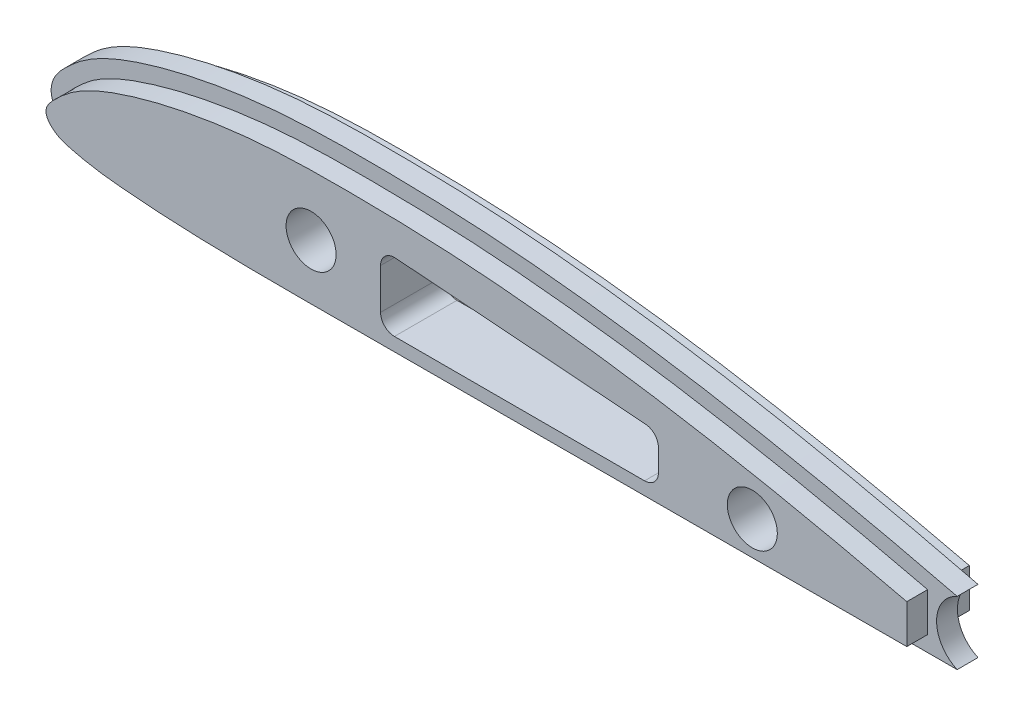
SolidWorks part; units mm, degrees
ref_plane "Front Plane" through (0, 0, 0) normal (0, 0, 1) x (1, 0, 0)
ref_plane "Top Plane" through (0, 0, 0) normal (0, 1, 0) x (1, 0, 0)
ref_plane "Right Plane" through (0, 0, 0) normal (1, 0, 0) x (0, 0, -1)
sketch "Sketch3" plane through (0, 0, 36) normal (0, 0, 1) x (1, 0, 0)
  line L0 (-17.5077, 7.0986) -> (-17.5077, -2.034) construction
  line L1 (-17.5077, 7.0986) -> (-17.5077, -2.034)
  circle A0 centre (-107.5077, 7.9994) radius 3.5 construction
  circle A1 centre (-107.5077, 7.9994) radius 3.5
  spline S0 degree 3 poles (2578.6537, 5862.2825) (2014.027, -6.3495) (990.936, -0.1904) (-36.5554, -2.0685) (-52.2047, -2.0959) (-64.7243, -2.119) (-74.1141, -2.1361) (-83.5035, -2.1545) (-92.8956, -2.1673) (-100.7151, -2.1812) (-106.9759, -2.2038) (-111.6807, -2.2071) (-116.3926, -2.1785) (-121.1131, -2.1002) (-125.8432, -1.946) (-129.7876, -1.7371) (-132.9528, -1.4988) (-135.2992, -1.2986) (-137.3062, -1.095) (-138.941, -0.8588) (-140.1679, -0.6381) (-141.3883, -0.367) (-142.5078, -0.1069) (-143.6199, 0.1874) (-144.5733, 0.5667) (-145.3185, 0.9606) (-146.0045, 1.4531) (-146.6187, 2.0134) (-147.1053, 2.5935) (-147.4573, 3.1709) (-147.6837, 3.6454) (-147.8752, 4.2833) (-147.9432, 4.9253) (-147.8905, 5.6127) (-147.6734, 6.4007) (-147.2979, 7.1351) (-146.8042, 7.8185) (-146.3098, 8.3773) (-145.6675, 9.0171) (-144.9341, 9.694) (-143.9278, 10.5554) (-142.8506, 11.3324) (-141.7288, 12.0232) (-140.2222, 12.8248) (-138.3122, 13.6733) (-136.0049, 14.5197) (-133.7043, 15.2528) (-131.3815, 15.9138) (-128.2582, 16.6871) (-124.3362, 17.4725) (-119.6006, 18.1902) (-114.8231, 18.6719) (-108.4622, 19.0054) (-100.5785, 19.0321) (-91.1325, 18.8431) (-81.6696, 18.2776) (-69.1255, 17.0496) (-53.5308, 14.8273) (539.3666, -100.5985) (899.837, -1164.8591) (3202.4957, 5810.2231) knots -10.067578 -10.067578 -10.067578 -10.067578 0.066238 0.128738 0.191238 0.222488 0.253738 0.284988 0.316238 0.347488 0.363113 0.378738 0.394363 0.409988 0.425613 0.441238 0.44905 0.456863 0.464675 0.468581 0.472488 0.476394 0.4803 0.484206 0.48616 0.488113 0.490066 0.492019 0.493972 0.494949 0.495925 0.496902 0.497878 0.498855 0.499831 0.501785 0.503738 0.505691 0.507644 0.51155 0.515456 0.519363 0.523269 0.527175 0.534988 0.5428 0.550613 0.558425 0.566238 0.581863 0.597488 0.613113 0.628738 0.659988 0.691238 0.722488 0.753738 0.816238 0.878738 6.758162 6.758162 6.758162 6.758162 only from (-17.5077, -2.034) to (-17.5077, 7.0986) construction
  spline S1 degree 3 poles (-17.5077, -2.034) (-17.5971, -2.0342) (-23.9464, -2.0455) (-36.5554, -2.0685) (-52.2047, -2.0959) (-64.7243, -2.119) (-74.1141, -2.1361) (-83.5035, -2.1545) (-92.8956, -2.1673) (-100.7151, -2.1812) (-106.9759, -2.2038) (-111.6807, -2.2071) (-116.3926, -2.1785) (-121.1131, -2.1002) (-125.8432, -1.946) (-129.7876, -1.7371) (-132.9528, -1.4988) (-135.2992, -1.2986) (-137.3062, -1.095) (-138.941, -0.8588) (-140.1679, -0.6381) (-141.3883, -0.367) (-142.5078, -0.1069) (-143.6199, 0.1874) (-144.5733, 0.5667) (-145.3185, 0.9606) (-146.0045, 1.4531) (-146.6187, 2.0134) (-147.1053, 2.5935) (-147.4573, 3.1709) (-147.6837, 3.6454) (-147.8752, 4.2833) (-147.9432, 4.9253) (-147.8905, 5.6127) (-147.6734, 6.4007) (-147.2979, 7.1351) (-146.8042, 7.8185) (-146.3098, 8.3773) (-145.6675, 9.0171) (-144.9341, 9.694) (-143.9278, 10.5554) (-142.8506, 11.3324) (-141.7288, 12.0232) (-140.2222, 12.8248) (-138.3122, 13.6733) (-136.0049, 14.5197) (-133.7043, 15.2528) (-131.3815, 15.9138) (-128.2582, 16.6871) (-124.3362, 17.4725) (-119.6006, 18.1902) (-114.8231, 18.6719) (-108.4622, 19.0054) (-100.5785, 19.0321) (-91.1325, 18.8431) (-81.6696, 18.2776) (-69.1255, 17.0496) (-53.5308, 14.8273) (-35.2974, 11.2776) (-23.331, 8.5279) (-17.5077, 7.0986) knots 0.065345 0.065345 0.065345 0.065345 0.066238 0.128738 0.191238 0.222488 0.253738 0.284988 0.316238 0.347488 0.363113 0.378738 0.394363 0.409988 0.425613 0.441238 0.44905 0.456863 0.464675 0.468581 0.472488 0.476394 0.4803 0.484206 0.48616 0.488113 0.490066 0.492019 0.493972 0.494949 0.495925 0.496902 0.497878 0.498855 0.499831 0.501785 0.503738 0.505691 0.507644 0.51155 0.515456 0.519363 0.523269 0.527175 0.534988 0.5428 0.550613 0.558425 0.566238 0.581863 0.597488 0.613113 0.628738 0.659988 0.691238 0.722488 0.753738 0.816238 0.878738 0.938393 0.938393 0.938393 0.938393
extrude "Boss-Extrude1" add sketch "Sketch3" along normal blind 4
sketch "Sketch4" plane through (0, 0, 40) normal (0, 0, 1) x (1, 0, 0)
  line L8 (-19.5077, -0.0375) -> (-19.5077, 5.5292) construction
  line L9 (-19.5077, -0.0375) -> (-19.5077, 5.5292)
  spline S0 degree 3 poles (7588.3721, 24816.6865) (508.1583, -325.7078) (274.7285, -72.9604) (-8.7039, 2.8051) (-14.5294, 4.3114) (-20.3656, 5.749) (-27.1741, 7.349) (-33.9781, 8.8726) (-44.6779, 11.0739) (-57.3308, 13.3728) (-71.0095, 15.2439) (-80.7996, 16.1817) (-89.6088, 16.7577) (-95.4883, 16.9494) (-102.3503, 17.0132) (-107.258, 17.0037) (-112.1692, 16.8306) (-117.0923, 16.4612) (-121.0358, 15.9731) (-125.9769, 15.1312) (-129.9439, 14.2596) (-133.8889, 13.1136) (-136.8933, 12.0983) (-139.3897, 11.029) (-141.3837, 9.9199) (-142.7986, 8.9179) (-143.8683, 7.9575) (-144.6863, 7.1841) (-145.2085, 6.616) (-145.5978, 6.0643) (-145.813, 5.6279) (-145.9496, 5.1105) (-145.9171, 4.6811) (-145.7813, 4.3037) (-145.6317, 4.0021) (-145.3221, 3.5593) (-144.843, 3.0846) (-144.0891, 2.535) (-143.0082, 2.0734) (-141.6202, 1.743) (-140.1624, 1.3998) (-138.7, 1.1241) (-136.7482, 0.848) (-134.3019, 0.6215) (-131.3684, 0.3793) (-125.498, 0.0064) (-115.6953, -0.2455) (-101.9687, -0.1771) (-89.2206, -0.1643) (-73.5301, -0.1352) (-57.8396, -0.1062) (-42.149, -0.0778) (-31.3617, -0.0594) (-22.5358, -0.0426) (-13.7099, -0.0276) (702.9944, 1.3342) (1416.7931, -17.4986) (2080.9229, 25690.8936) knots -2.879038 -2.879038 -2.879038 -2.879038 0.020105 0.030145 0.050191 0.08018 0.090156 0.12002 0.149793 0.199219 0.248396 0.287604 0.297393 0.336535 0.346322 0.365908 0.385531 0.395376 0.415192 0.425184 0.445412 0.455711 0.466191 0.477055 0.482787 0.488946 0.494316 0.497126 0.500187 0.502001 0.50385 0.50502 0.507318 0.507987 0.509024 0.510668 0.513358 0.515716 0.519949 0.524973 0.529954 0.534903 0.539824 0.54963 0.559425 0.569214 0.608356 0.657307 0.706263 0.735637 0.813967 0.862923 0.892297 0.92167 0.951044 0.980418 8.077484 8.077484 8.077484 8.077484 only from (1.0061, 0.1754) to (1, -0.0006) construction
  spline S1 degree 3 poles (-19.5077, 5.5292) (-20.4438, 5.7568) (-22.3518, 6.2157) (-27.1741, 7.349) (-33.9781, 8.8726) (-44.6779, 11.0739) (-57.3308, 13.3728) (-71.0095, 15.2439) (-80.7996, 16.1817) (-89.6088, 16.7577) (-95.4883, 16.9494) (-102.3503, 17.0132) (-107.258, 17.0037) (-112.1692, 16.8306) (-117.0923, 16.4612) (-121.0358, 15.9731) (-125.9769, 15.1312) (-129.9439, 14.2596) (-133.8889, 13.1136) (-136.8933, 12.0983) (-139.3897, 11.029) (-141.3837, 9.9199) (-142.7986, 8.9179) (-143.8683, 7.9575) (-144.6863, 7.1841) (-145.2085, 6.616) (-145.5978, 6.0643) (-145.813, 5.6279) (-145.9496, 5.1105) (-145.9171, 4.6811) (-145.7813, 4.3037) (-145.6317, 4.0021) (-145.3221, 3.5593) (-144.843, 3.0846) (-144.0891, 2.535) (-143.0082, 2.0734) (-141.6202, 1.743) (-140.1624, 1.3998) (-138.7, 1.1241) (-136.7482, 0.848) (-134.3019, 0.6215) (-131.3684, 0.3793) (-125.498, 0.0064) (-115.6953, -0.2455) (-101.9687, -0.1771) (-89.2206, -0.1643) (-73.5301, -0.1352) (-57.8396, -0.1062) (-42.149, -0.0778) (-31.3617, -0.0594) (-24.4684, -0.0463) (-20.5171, -0.0393) (-19.5077, -0.0375) knots 0.070562 0.070562 0.070562 0.070562 0.08018 0.090156 0.12002 0.149793 0.199219 0.248396 0.287604 0.297393 0.336535 0.346322 0.365908 0.385531 0.395376 0.415192 0.425184 0.445412 0.455711 0.466191 0.477055 0.482787 0.488946 0.494316 0.497126 0.500187 0.502001 0.50385 0.50502 0.507318 0.507987 0.509024 0.510668 0.513358 0.515716 0.519949 0.524973 0.529954 0.534903 0.539824 0.54963 0.559425 0.569214 0.608356 0.657307 0.706263 0.735637 0.813967 0.862923 0.892297 0.92167 0.931748 0.931748 0.931748 0.931748
extrude "Boss-Extrude2" add sketch "Sketch4" along normal blind 3
sketch "Sketch6" plane through (0, 0, 40) normal (0, 0, 1) x (1, 0, 0)
  line L1 (-17.5077, -2.034) -> (-17.5077, 7.0986)
  line L2 (-17.5077, -2.034) -> (-17.5077, 7.0986)
  spline S1 degree 3 poles (1849.108, 2047.2656) (715.5466, -712.3066) (399.8034, -73.4282) (-53.5308, 14.8273) (-69.1255, 17.0496) (-81.6696, 18.2776) (-91.1325, 18.8431) (-100.5785, 19.0321) (-108.4622, 19.0054) (-114.8231, 18.6719) (-119.6006, 18.1902) (-124.3362, 17.4725) (-128.2582, 16.6871) (-131.3815, 15.9138) (-133.7043, 15.2528) (-136.0049, 14.5197) (-138.3122, 13.6733) (-140.2222, 12.8248) (-141.7288, 12.0232) (-142.8506, 11.3324) (-143.9278, 10.5554) (-144.9341, 9.694) (-145.6675, 9.0171) (-146.3098, 8.3773) (-146.8042, 7.8185) (-147.2979, 7.1351) (-147.6734, 6.4007) (-147.8905, 5.6127) (-147.9432, 4.9253) (-147.8752, 4.2833) (-147.6837, 3.6454) (-147.4573, 3.1709) (-147.1053, 2.5935) (-146.6187, 2.0134) (-146.0045, 1.4531) (-145.3185, 0.9606) (-144.5733, 0.5667) (-143.6199, 0.1874) (-142.5078, -0.1069) (-141.3883, -0.367) (-140.1679, -0.6381) (-138.941, -0.8588) (-137.3062, -1.095) (-135.2992, -1.2986) (-132.9528, -1.4988) (-129.7876, -1.7371) (-125.8432, -1.946) (-121.1131, -2.1002) (-116.3926, -2.1785) (-111.6807, -2.2071) (-106.9759, -2.2038) (-100.7151, -2.1812) (-92.8956, -2.1673) (-83.5035, -2.1545) (-74.1141, -2.1361) (-64.7243, -2.119) (-52.2047, -2.0959) (-36.5554, -2.0685) (675.8455, -0.7663) (1382.8755, -3.3128) (1935.6442, 1919.1904) knots -4.341032 -4.341032 -4.341032 -4.341032 0.125 0.1875 0.25 0.28125 0.3125 0.34375 0.375 0.390625 0.40625 0.421875 0.4375 0.445312 0.453125 0.460937 0.46875 0.476562 0.480469 0.484375 0.488281 0.492187 0.496094 0.498047 0.5 0.501953 0.503906 0.504883 0.505859 0.506836 0.507812 0.508789 0.509766 0.511719 0.513672 0.515625 0.517578 0.519531 0.523438 0.527344 0.53125 0.535156 0.539062 0.546875 0.554688 0.5625 0.578125 0.59375 0.609375 0.625 0.640625 0.65625 0.6875 0.71875 0.75 0.78125 0.8125 0.875 0.9375 7.925347 7.925347 7.925347 7.925347 only from (-17.5077, 7.0986) to (-17.5077, -2.034)
  spline S2 degree 3 poles (-17.5077, 7.0986) (-23.331, 8.5279) (-35.2974, 11.2776) (-53.5308, 14.8273) (-69.1255, 17.0496) (-81.6696, 18.2776) (-91.1325, 18.8431) (-100.5785, 19.0321) (-108.4622, 19.0054) (-114.8231, 18.6719) (-119.6006, 18.1902) (-124.3362, 17.4725) (-128.2582, 16.6871) (-131.3815, 15.9138) (-133.7043, 15.2528) (-136.0049, 14.5197) (-138.3122, 13.6733) (-140.2222, 12.8248) (-141.7288, 12.0232) (-142.8506, 11.3324) (-143.9278, 10.5554) (-144.9341, 9.694) (-145.6675, 9.0171) (-146.3098, 8.3773) (-146.8042, 7.8185) (-147.2979, 7.1351) (-147.6734, 6.4007) (-147.8905, 5.6127) (-147.9432, 4.9253) (-147.8752, 4.2833) (-147.6837, 3.6454) (-147.4573, 3.1709) (-147.1053, 2.5935) (-146.6187, 2.0134) (-146.0045, 1.4531) (-145.3185, 0.9606) (-144.5733, 0.5667) (-143.6199, 0.1874) (-142.5078, -0.1069) (-141.3883, -0.367) (-140.1679, -0.6381) (-138.941, -0.8588) (-137.3062, -1.095) (-135.2992, -1.2986) (-132.9528, -1.4988) (-129.7876, -1.7371) (-125.8432, -1.946) (-121.1131, -2.1002) (-116.3926, -2.1785) (-111.6807, -2.2071) (-106.9759, -2.2038) (-100.7151, -2.1812) (-92.8956, -2.1673) (-83.5035, -2.1545) (-74.1141, -2.1361) (-64.7243, -2.119) (-52.2047, -2.0959) (-36.5554, -2.0685) (-23.9464, -2.0455) (-17.5971, -2.0342) (-17.5077, -2.034) knots 0.065345 0.065345 0.065345 0.065345 0.125 0.1875 0.25 0.28125 0.3125 0.34375 0.375 0.390625 0.40625 0.421875 0.4375 0.445312 0.453125 0.460937 0.46875 0.476562 0.480469 0.484375 0.488281 0.492187 0.496094 0.498047 0.5 0.501953 0.503906 0.504883 0.505859 0.506836 0.507812 0.508789 0.509766 0.511719 0.513672 0.515625 0.517578 0.519531 0.523438 0.527344 0.53125 0.535156 0.539062 0.546875 0.554688 0.5625 0.578125 0.59375 0.609375 0.625 0.640625 0.65625 0.6875 0.71875 0.75 0.78125 0.8125 0.875 0.9375 0.938393 0.938393 0.938393 0.938393
  dimension "D1" = 0
extrude "Cut-Extrude1" cut sketch "Sketch6" against normal through all
sketch "Sketch7" plane through (0, 0, 40) normal (0, 0, -1) x (-1, 0, 0)
  line L0 (17.5077, 7.0986) -> (17.5077, -2.034) construction
  line L1 (17.5077, 7.0986) -> (17.5077, -2.034)
  spline S0 degree 3 poles (-1935.6474, 1919.198) (-1382.8774, -3.3129) (-675.8464, -0.7663) (36.5554, -2.0685) (52.2047, -2.0959) (64.7243, -2.119) (74.1141, -2.1361) (83.5035, -2.1545) (92.8956, -2.1673) (100.7151, -2.1812) (106.9759, -2.2038) (111.6807, -2.2071) (116.3926, -2.1785) (121.1131, -2.1002) (125.8432, -1.946) (129.7876, -1.7371) (132.9528, -1.4988) (135.2992, -1.2986) (137.3062, -1.095) (138.941, -0.8588) (140.1679, -0.6381) (141.3883, -0.367) (142.5078, -0.1069) (143.6199, 0.1874) (144.5733, 0.5667) (145.3185, 0.9606) (146.0045, 1.4531) (146.6187, 2.0134) (147.1053, 2.5935) (147.4573, 3.1709) (147.6837, 3.6454) (147.8752, 4.2833) (147.9432, 4.9253) (147.8905, 5.6127) (147.6734, 6.4007) (147.2979, 7.1351) (146.8042, 7.8185) (146.3098, 8.3773) (145.6675, 9.0171) (144.9341, 9.694) (143.9278, 10.5554) (142.8506, 11.3324) (141.7288, 12.0232) (140.2222, 12.8248) (138.3122, 13.6733) (136.0049, 14.5197) (133.7043, 15.2528) (131.3815, 15.9138) (128.2582, 16.6871) (124.3362, 17.4725) (119.6006, 18.1902) (114.8231, 18.6719) (108.4622, 19.0054) (100.5785, 19.0321) (91.1325, 18.8431) (81.6696, 18.2776) (69.1255, 17.0496) (53.5308, 14.8273) (-399.8012, -73.4278) (-715.5435, -712.3002) (-1849.0908, 2047.2238) knots -6.921618 -6.921618 -6.921618 -6.921618 0.066238 0.128738 0.191238 0.222488 0.253738 0.284988 0.316238 0.347488 0.363113 0.378738 0.394363 0.409988 0.425613 0.441238 0.44905 0.456863 0.464675 0.468581 0.472488 0.476394 0.4803 0.484206 0.48616 0.488113 0.490066 0.492019 0.493972 0.494949 0.495925 0.496902 0.497878 0.498855 0.499831 0.501785 0.503738 0.505691 0.507644 0.51155 0.515456 0.519363 0.523269 0.527175 0.534988 0.5428 0.550613 0.558425 0.566238 0.581863 0.597488 0.613113 0.628738 0.659988 0.691238 0.722488 0.753738 0.816238 0.878738 5.344747 5.344747 5.344747 5.344747 only from (17.5077, -2.034) to (17.5077, 7.0986) construction
  spline S1 degree 3 poles (17.5077, -2.034) (17.5971, -2.0342) (23.9464, -2.0455) (36.5554, -2.0685) (52.2047, -2.0959) (64.7243, -2.119) (74.1141, -2.1361) (83.5035, -2.1545) (92.8956, -2.1673) (100.7151, -2.1812) (106.9759, -2.2038) (111.6807, -2.2071) (116.3926, -2.1785) (121.1131, -2.1002) (125.8432, -1.946) (129.7876, -1.7371) (132.9528, -1.4988) (135.2992, -1.2986) (137.3062, -1.095) (138.941, -0.8588) (140.1679, -0.6381) (141.3883, -0.367) (142.5078, -0.1069) (143.6199, 0.1874) (144.5733, 0.5667) (145.3185, 0.9606) (146.0045, 1.4531) (146.6187, 2.0134) (147.1053, 2.5935) (147.4573, 3.1709) (147.6837, 3.6454) (147.8752, 4.2833) (147.9432, 4.9253) (147.8905, 5.6127) (147.6734, 6.4007) (147.2979, 7.1351) (146.8042, 7.8185) (146.3098, 8.3773) (145.6675, 9.0171) (144.9341, 9.694) (143.9278, 10.5554) (142.8506, 11.3324) (141.7288, 12.0232) (140.2222, 12.8248) (138.3122, 13.6733) (136.0049, 14.5197) (133.7043, 15.2528) (131.3815, 15.9138) (128.2582, 16.6871) (124.3362, 17.4725) (119.6006, 18.1902) (114.8231, 18.6719) (108.4622, 19.0054) (100.5785, 19.0321) (91.1325, 18.8431) (81.6696, 18.2776) (69.1255, 17.0496) (53.5308, 14.8273) (35.2974, 11.2776) (23.331, 8.5279) (17.5077, 7.0986) knots 0.065345 0.065345 0.065345 0.065345 0.066238 0.128738 0.191238 0.222488 0.253738 0.284988 0.316238 0.347488 0.363113 0.378738 0.394363 0.409988 0.425613 0.441238 0.44905 0.456863 0.464675 0.468581 0.472488 0.476394 0.4803 0.484206 0.48616 0.488113 0.490066 0.492019 0.493972 0.494949 0.495925 0.496902 0.497878 0.498855 0.499831 0.501785 0.503738 0.505691 0.507644 0.51155 0.515456 0.519363 0.523269 0.527175 0.534988 0.5428 0.550613 0.558425 0.566238 0.581863 0.597488 0.613113 0.628738 0.659988 0.691238 0.722488 0.753738 0.816238 0.878738 0.938393 0.938393 0.938393 0.938393
extrude "Boss-Extrude4" add sketch "Sketch7" along normal blind 3
sketch "Sketch8" plane through (0, 0, 37) normal (0, 0, -1) x (-1, 0, 0)
  line L1 (19.5077, 5.5292) -> (19.5077, -0.0375)
  line L2 (19.5077, 5.5292) -> (19.5077, -0.0375)
  spline S1 degree 3 poles (-1386.8586, 2447.2657) (-920.0116, -6.1198) (-445.7888, 0.849) (31.3617, -0.0594) (42.149, -0.0778) (57.8396, -0.1062) (73.5301, -0.1352) (89.2206, -0.1643) (101.9687, -0.1771) (115.6953, -0.2455) (125.498, 0.0064) (131.3684, 0.3793) (134.3019, 0.6215) (136.7482, 0.848) (138.7, 1.1241) (140.1624, 1.3998) (141.6202, 1.743) (143.0082, 2.0734) (144.0891, 2.535) (144.843, 3.0846) (145.3221, 3.5593) (145.6317, 4.0021) (145.7813, 4.3037) (145.9171, 4.6811) (145.9496, 5.1105) (145.813, 5.6279) (145.5978, 6.0643) (145.2085, 6.616) (144.6863, 7.1841) (143.8683, 7.9575) (142.7986, 8.9179) (141.3837, 9.9199) (139.3897, 11.029) (136.8933, 12.0983) (133.8889, 13.1136) (129.9439, 14.2596) (125.9769, 15.1312) (121.0358, 15.9731) (117.0923, 16.4612) (112.1692, 16.8306) (107.258, 17.0037) (102.3503, 17.0132) (95.4883, 16.9494) (89.6088, 16.7577) (80.7996, 16.1817) (71.0095, 15.2439) (57.3308, 13.3728) (44.6779, 11.0739) (33.9781, 8.8726) (27.1741, 7.349) (-277.492, -64.2503) (-519.7765, -384.6594) (-1220.5185, 2634.6577) knots -4.624642 -4.624642 -4.624642 -4.624642 0.08064 0.110014 0.139387 0.188343 0.266673 0.296047 0.345003 0.393954 0.433096 0.442885 0.45268 0.462486 0.467407 0.472356 0.477337 0.482361 0.486594 0.488952 0.491642 0.493286 0.494324 0.494992 0.49729 0.49846 0.500309 0.502123 0.505184 0.507994 0.513364 0.519523 0.525256 0.536119 0.546599 0.556898 0.577126 0.587118 0.606934 0.616779 0.636402 0.655988 0.665775 0.704917 0.714706 0.753914 0.803091 0.852517 0.88229 0.912154 0.92213 4.007029 4.007029 4.007029 4.007029 only from (19.5077, -0.0375) to (19.5077, 5.5292)
  spline S2 degree 3 poles (19.5077, -0.0375) (20.5171, -0.0393) (24.4684, -0.0463) (31.3617, -0.0594) (42.149, -0.0778) (57.8396, -0.1062) (73.5301, -0.1352) (89.2206, -0.1643) (101.9687, -0.1771) (115.6953, -0.2455) (125.498, 0.0064) (131.3684, 0.3793) (134.3019, 0.6215) (136.7482, 0.848) (138.7, 1.1241) (140.1624, 1.3998) (141.6202, 1.743) (143.0082, 2.0734) (144.0891, 2.535) (144.843, 3.0846) (145.3221, 3.5593) (145.6317, 4.0021) (145.7813, 4.3037) (145.9171, 4.6811) (145.9496, 5.1105) (145.813, 5.6279) (145.5978, 6.0643) (145.2085, 6.616) (144.6863, 7.1841) (143.8683, 7.9575) (142.7986, 8.9179) (141.3837, 9.9199) (139.3897, 11.029) (136.8933, 12.0983) (133.8889, 13.1136) (129.9439, 14.2596) (125.9769, 15.1312) (121.0358, 15.9731) (117.0923, 16.4612) (112.1692, 16.8306) (107.258, 17.0037) (102.3503, 17.0132) (95.4883, 16.9494) (89.6088, 16.7577) (80.7996, 16.1817) (71.0095, 15.2439) (57.3308, 13.3728) (44.6779, 11.0739) (33.9781, 8.8726) (27.1741, 7.349) (22.3518, 6.2157) (20.4438, 5.7568) (19.5077, 5.5292) knots 0.070562 0.070562 0.070562 0.070562 0.08064 0.110014 0.139387 0.188343 0.266673 0.296047 0.345003 0.393954 0.433096 0.442885 0.45268 0.462486 0.467407 0.472356 0.477337 0.482361 0.486594 0.488952 0.491642 0.493286 0.494324 0.494992 0.49729 0.49846 0.500309 0.502123 0.505184 0.507994 0.513364 0.519523 0.525256 0.536119 0.546599 0.556898 0.577126 0.587118 0.606934 0.616779 0.636402 0.655988 0.665775 0.704917 0.714706 0.753914 0.803091 0.852517 0.88229 0.912154 0.92213 0.931748 0.931748 0.931748 0.931748
  dimension "D1" = 0
extrude "Boss-Extrude5" add sketch "Sketch8" along normal blind 3
sketch "Sketch9" plane through (0, 0, 43) normal (0, 0, 1) x (1, 0, 0)
  line L0 (-59.5077, 1.9994) -> (-95.5077, 1.9994) construction
  line L1 (-95.3581, 11.8382) -> (-59.3581, 9.1382) construction
  line L2 (-97.5077, 3.9994) -> (-97.5077, 9.8438) construction
  line L3 (-59.5077, 1.9994) -> (-95.5077, 1.9994)
  line L4 (-95.3581, 11.8382) -> (-59.3581, 9.1382)
  line L5 (-97.5077, 3.9994) -> (-97.5077, 9.8438)
  line L6 (-57.5077, 7.1438) -> (-57.5077, 3.9994) construction
  line L7 (-57.5077, 7.1438) -> (-57.5077, 3.9994)
  circle A1 centre (-107.5077, 7.9994) radius 3.6
  arc A2 (-57.5077, 7.1438) -> (-59.3581, 9.1382) centre (-59.5077, 7.1438) ccw construction
  arc A3 (-59.5077, 1.9994) -> (-57.5077, 3.9994) centre (-59.5077, 3.9994) ccw construction
  arc A4 (-97.5077, 3.9994) -> (-95.5077, 1.9994) centre (-95.5077, 3.9994) ccw construction
  arc A5 (-95.3581, 11.8382) -> (-97.5077, 9.8438) centre (-95.5077, 9.8438) ccw construction
  arc A6 (-57.5077, 7.1438) -> (-59.3581, 9.1382) centre (-59.5077, 7.1438) ccw
  arc A7 (-59.5077, 1.9994) -> (-57.5077, 3.9994) centre (-59.5077, 3.9994) ccw
  arc A8 (-97.5077, 3.9994) -> (-95.5077, 1.9994) centre (-95.5077, 3.9994) ccw
  arc A9 (-95.3581, 11.8382) -> (-97.5077, 9.8438) centre (-95.5077, 9.8438) ccw
  circle A11 centre (-43.9939, 4.9994) radius 3.6
extrude "Cut-Extrude2" cut sketch "Sketch9" against normal up to surface (9 mm away) up to face at (-82.6927, 3.6746, 34)
sketch "Sketch10" plane through (0, 0, 40) normal (0, 0, 1) x (1, 0, 0)
  line L0 (-17.5077, 7.0986) -> (-17.5077, -2.034)
  arc A0 (-17.5077, 7.0986) -> (-17.5077, -2.034) centre (-15.4708, 2.5323) ccw construction
  arc A1 (-17.5077, 7.0986) -> (-17.5077, -2.034) centre (-15.4708, 2.5323) ccw
extrude "Cut-Extrude3" cut sketch "Sketch10" against normal through all both and the other way through all
sketch "Sketch11" plane through (0, 0, 43) normal (0, 0, 1) x (1, 0, 0)
  line L0 (-21.5077, 6.6228) -> (-21.5077, -0.5387)
  line L3 (-19.3398, -0.5387) -> (-19.3398, 6.6228)
  line L4 (-21.5077, 6.6228) -> (-19.3398, 6.6228)
  line L5 (-21.5077, -0.5387) -> (-19.3398, -0.5387)
extrude "Cut-Extrude6" cut sketch "Sketch11" against normal up to surface (3 mm away) up to face at (-18.7848, 2.8426, 40)
sketch "Sketch12" plane through (0, 0, 34) normal (0, 0, -1) x (-1, 0, 0)
  line L4 (21.5077, -0.5387) -> (21.5077, 6.6228)
  line L5 (19.3398, -0.5387) -> (21.5077, -0.5387)
  line L6 (19.3398, 6.6228) -> (19.3398, -0.5387)
  line L7 (21.5077, 6.6228) -> (19.3398, 6.6228)
  line L8 (21.5077, -0.5387) -> (21.5077, 6.6228)
  line L9 (19.3398, -0.5387) -> (21.5077, -0.5387)
  line L10 (19.3398, 6.6228) -> (19.3398, -0.5387)
  line L11 (21.5077, 6.6228) -> (19.3398, 6.6228)
  dimension "D1" = 0
extrude "Cut-Extrude7" cut sketch "Sketch12" against normal up to surface (3 mm away) up to face at (-44.0587, 2.6574, 37)
sketch "Sketch14" plane through (0, 0, 34) normal (0, 0, -1) x (-1, 0, 0)
  line L8 (0.1965, 0.2471) -> (1.9943, 0.2439)
  line L9 (2.0597, 0.7559) -> (0.1965, 0.2471)
  line L12 (21.7577, 5.8144) -> (21.7577, 0.2085)
  arc A1 (17.5077, -2.034) -> (17.5077, 7.0986) centre (15.4708, 2.5323) ccw
  arc A2 (17.5077, -2.034) -> (17.5077, 7.0986) centre (15.4708, 2.5323) ccw
  spline S1 degree 3 poles (-2168.1099, 2891.7414) (-1587.7739, -4.1313) (-778.1565, -0.5793) (36.5554, -2.0685) (52.2047, -2.0959) (64.7243, -2.119) (74.1141, -2.1361) (83.5035, -2.1545) (92.8956, -2.1673) (100.7151, -2.1812) (106.9759, -2.2038) (111.6807, -2.2071) (116.3926, -2.1785) (121.1131, -2.1002) (125.8432, -1.946) (129.7876, -1.7371) (132.9528, -1.4988) (135.2992, -1.2986) (137.3062, -1.095) (138.941, -0.8588) (140.1679, -0.6381) (141.3883, -0.367) (142.5078, -0.1069) (143.6199, 0.1874) (144.5733, 0.5667) (145.3185, 0.9606) (146.0045, 1.4531) (146.6187, 2.0134) (147.1053, 2.5935) (147.4573, 3.1709) (147.6837, 3.6454) (147.8752, 4.2833) (147.9432, 4.9253) (147.8905, 5.6127) (147.6734, 6.4007) (147.2979, 7.1351) (146.8042, 7.8185) (146.3098, 8.3773) (145.6675, 9.0171) (144.9341, 9.694) (143.9278, 10.5554) (142.8506, 11.3324) (141.7288, 12.0232) (140.2222, 12.8248) (138.3122, 13.6733) (136.0049, 14.5197) (133.7043, 15.2528) (131.3815, 15.9138) (128.2582, 16.6871) (124.3362, 17.4725) (119.6006, 18.1902) (114.8231, 18.6719) (108.4622, 19.0054) (100.5785, 19.0321) (91.1325, 18.8431) (81.6696, 18.2776) (69.1255, 17.0496) (53.5308, 14.8273) (-443.7991, -81.9934) (-776.4054, -843.365) (-2213.8717, 2978.3065) knots -7.943117 -7.943117 -7.943117 -7.943117 0.066238 0.128738 0.191238 0.222488 0.253738 0.284988 0.316238 0.347488 0.363113 0.378738 0.394363 0.409988 0.425613 0.441238 0.44905 0.456863 0.464675 0.468581 0.472488 0.476394 0.4803 0.484206 0.48616 0.488113 0.490066 0.492019 0.493972 0.494949 0.495925 0.496902 0.497878 0.498855 0.499831 0.501785 0.503738 0.505691 0.507644 0.51155 0.515456 0.519363 0.523269 0.527175 0.534988 0.5428 0.550613 0.558425 0.566238 0.581863 0.597488 0.613113 0.628738 0.659988 0.691238 0.722488 0.753738 0.816238 0.878738 5.790325 5.790325 5.790325 5.790325 only from (17.5077, -2.034) to (17.5077, 7.0986)
  spline S2 degree 3 poles (17.5077, -2.034) (17.5971, -2.0342) (23.9464, -2.0455) (36.5554, -2.0685) (52.2047, -2.0959) (64.7243, -2.119) (74.1141, -2.1361) (83.5035, -2.1545) (92.8956, -2.1673) (100.7151, -2.1812) (106.9759, -2.2038) (111.6807, -2.2071) (116.3926, -2.1785) (121.1131, -2.1002) (125.8432, -1.946) (129.7876, -1.7371) (132.9528, -1.4988) (135.2992, -1.2986) (137.3062, -1.095) (138.941, -0.8588) (140.1679, -0.6381) (141.3883, -0.367) (142.5078, -0.1069) (143.6199, 0.1874) (144.5733, 0.5667) (145.3185, 0.9606) (146.0045, 1.4531) (146.6187, 2.0134) (147.1053, 2.5935) (147.4573, 3.1709) (147.6837, 3.6454) (147.8752, 4.2833) (147.9432, 4.9253) (147.8905, 5.6127) (147.6734, 6.4007) (147.2979, 7.1351) (146.8042, 7.8185) (146.3098, 8.3773) (145.6675, 9.0171) (144.9341, 9.694) (143.9278, 10.5554) (142.8506, 11.3324) (141.7288, 12.0232) (140.2222, 12.8248) (138.3122, 13.6733) (136.0049, 14.5197) (133.7043, 15.2528) (131.3815, 15.9138) (128.2582, 16.6871) (124.3362, 17.4725) (119.6006, 18.1902) (114.8231, 18.6719) (108.4622, 19.0054) (100.5785, 19.0321) (91.1325, 18.8431) (81.6696, 18.2776) (69.1255, 17.0496) (53.5308, 14.8273) (35.2974, 11.2776) (23.331, 8.5279) (17.5077, 7.0986) knots 0.065345 0.065345 0.065345 0.065345 0.066238 0.128738 0.191238 0.222488 0.253738 0.284988 0.316238 0.347488 0.363113 0.378738 0.394363 0.409988 0.425613 0.441238 0.44905 0.456863 0.464675 0.468581 0.472488 0.476394 0.4803 0.484206 0.48616 0.488113 0.490066 0.492019 0.493972 0.494949 0.495925 0.496902 0.497878 0.498855 0.499831 0.501785 0.503738 0.505691 0.507644 0.51155 0.515456 0.519363 0.523269 0.527175 0.534988 0.5428 0.550613 0.558425 0.566238 0.581863 0.597488 0.613113 0.628738 0.659988 0.691238 0.722488 0.753738 0.816238 0.878738 0.938393 0.938393 0.938393 0.938393
  spline S3 degree 3 poles (-3454.9534, -1594.114) (-2323.8473, 5.4591) (-1145.5181, 2.3065) (38.7901, 0.1778) (57.188, 0.1449) (72.5196, 0.1171) (84.7849, 0.0931) (93.9835, 0.0819) (103.1836, 0.0616) (110.8482, 0.0336) (116.9777, 0.0786) (121.5735, 0.1623) (126.1655, 0.3208) (129.9882, 0.5307) (133.0401, 0.7666) (135.3307, 0.9631) (137.6083, 1.2031) (139.4856, 1.5117) (140.9704, 1.8466) (142.0924, 2.1068) (143.178, 2.4067) (144.1782, 2.8689) (145.0251, 3.565) (145.6778, 4.4512) (145.7044, 5.4436) (145.1066, 6.373) (144.3373, 7.1816) (143.4941, 7.9604) (142.6379, 8.7027) (141.422, 9.5981) (139.7821, 10.5463) (137.7041, 11.489) (135.5625, 12.2917) (132.6552, 13.2342) (128.9684, 14.2359) (124.4735, 15.1602) (119.9399, 15.8743) (115.3785, 16.3691) (109.2691, 16.733) (101.6096, 16.7888) (92.4172, 16.633) (83.2405, 16.141) (74.0879, 15.2916) (64.9619, 14.1797) (52.8412, 12.3593) (37.7826, 9.4994) (-321.3624, -71.443) (-593.78, -490.5689) (-1286.3146, 3667.0627) knots -11.630495 -11.630495 -11.630495 -11.630495 0.071582 0.132813 0.194043 0.255273 0.285888 0.316503 0.347118 0.377734 0.393041 0.408349 0.423656 0.438964 0.446618 0.454271 0.461925 0.469579 0.473406 0.477233 0.48106 0.484887 0.488713 0.49254 0.496367 0.500194 0.504021 0.507848 0.511675 0.515502 0.523155 0.530809 0.538463 0.546117 0.561424 0.576732 0.592039 0.607347 0.622655 0.65327 0.683885 0.7145 0.745115 0.77573 0.806345 0.867576 0.928806 4.483446 4.483446 4.483446 4.483446 only from (1.9943, 0.2439) to (2.0597, 0.7559)
  spline S4 degree 3 poles (21.7577, 0.2085) (27.4352, 0.1982) (39.2453, 0.177) (57.188, 0.1449) (72.5196, 0.1171) (84.7849, 0.0931) (93.9835, 0.0819) (103.1836, 0.0616) (110.8482, 0.0336) (116.9777, 0.0786) (121.5735, 0.1623) (126.1655, 0.3208) (129.9882, 0.5307) (133.0401, 0.7666) (135.3307, 0.9631) (137.6083, 1.2031) (139.4856, 1.5117) (140.9704, 1.8466) (142.0924, 2.1068) (143.178, 2.4067) (144.1782, 2.8689) (145.0251, 3.565) (145.6778, 4.4512) (145.7044, 5.4436) (145.1066, 6.373) (144.3373, 7.1816) (143.4941, 7.9604) (142.6379, 8.7027) (141.422, 9.5981) (139.7821, 10.5463) (137.7041, 11.489) (135.5625, 12.2917) (132.6552, 13.2342) (128.9684, 14.2359) (124.4735, 15.1602) (119.9399, 15.8743) (115.3785, 16.3691) (109.2691, 16.733) (101.6096, 16.7888) (92.4172, 16.633) (83.2405, 16.141) (74.0879, 15.2916) (64.9619, 14.1797) (52.8412, 12.3593) (38.4204, 9.6206) (27.0885, 7.0881) (21.7577, 5.8144) knots 0.076127 0.076127 0.076127 0.076127 0.132813 0.194043 0.255273 0.285888 0.316503 0.347118 0.377734 0.393041 0.408349 0.423656 0.438964 0.446618 0.454271 0.461925 0.469579 0.473406 0.477233 0.48106 0.484887 0.488713 0.49254 0.496367 0.500194 0.504021 0.507848 0.511675 0.515502 0.523155 0.530809 0.538463 0.546117 0.561424 0.576732 0.592039 0.607347 0.622655 0.65327 0.683885 0.7145 0.745115 0.77573 0.806345 0.867576 0.922323 0.922323 0.922323 0.922323
  dimension "D1" = 0
  dimension "D2" = 0
extrude "Cut-Extrude9" cut sketch "Sketch14" against normal up to surface (3 mm away) up to face at (-83.6927, 3.7943, 37)
sketch "Sketch15" plane through (0, 0, 43) normal (0, 0, 1) x (1, 0, 0)
  line L1 (-21.7577, 0.2085) -> (-21.7577, 5.8144)
  line L2 (-21.7577, 0.2085) -> (-21.7577, 5.8144)
  arc A1 (-17.5077, 7.0986) -> (-17.5077, -2.034) centre (-15.4708, 2.5323) ccw
  arc A2 (-17.5077, 7.0986) -> (-17.5077, -2.034) centre (-15.4708, 2.5323) ccw
  spline S1 degree 3 poles (2213.8577, 2978.2694) (776.4033, -843.3601) (443.7975, -81.9931) (-53.5308, 14.8273) (-69.1255, 17.0496) (-81.6696, 18.2776) (-91.1325, 18.8431) (-100.5785, 19.0321) (-108.4622, 19.0054) (-114.8231, 18.6719) (-119.6006, 18.1902) (-124.3362, 17.4725) (-128.2582, 16.6871) (-131.3815, 15.9138) (-133.7043, 15.2528) (-136.0049, 14.5197) (-138.3122, 13.6733) (-140.2222, 12.8248) (-141.7288, 12.0232) (-142.8506, 11.3324) (-143.9278, 10.5554) (-144.9341, 9.694) (-145.6675, 9.0171) (-146.3098, 8.3773) (-146.8042, 7.8185) (-147.2979, 7.1351) (-147.6734, 6.4007) (-147.8905, 5.6127) (-147.9432, 4.9253) (-147.8752, 4.2833) (-147.6837, 3.6454) (-147.4573, 3.1709) (-147.1053, 2.5935) (-146.6187, 2.0134) (-146.0045, 1.4531) (-145.3185, 0.9606) (-144.5733, 0.5667) (-143.6199, 0.1874) (-142.5078, -0.1069) (-141.3883, -0.367) (-140.1679, -0.6381) (-138.941, -0.8588) (-137.3062, -1.095) (-135.2992, -1.2986) (-132.9528, -1.4988) (-129.7876, -1.7371) (-125.8432, -1.946) (-121.1131, -2.1002) (-116.3926, -2.1785) (-111.6807, -2.2071) (-106.9759, -2.2038) (-100.7151, -2.1812) (-92.8956, -2.1673) (-83.5035, -2.1545) (-74.1141, -2.1361) (-64.7243, -2.119) (-52.2047, -2.0959) (-36.5554, -2.0685) (778.1573, -0.5793) (1587.7755, -4.1313) (2168.1101, 2891.7501) knots -4.786572 -4.786572 -4.786572 -4.786572 0.125 0.1875 0.25 0.28125 0.3125 0.34375 0.375 0.390625 0.40625 0.421875 0.4375 0.445312 0.453125 0.460937 0.46875 0.476562 0.480469 0.484375 0.488281 0.492187 0.496094 0.498047 0.5 0.501953 0.503906 0.504883 0.505859 0.506836 0.507812 0.508789 0.509766 0.511719 0.513672 0.515625 0.517578 0.519531 0.523438 0.527344 0.53125 0.535156 0.539062 0.546875 0.554688 0.5625 0.578125 0.59375 0.609375 0.625 0.640625 0.65625 0.6875 0.71875 0.75 0.78125 0.8125 0.875 0.9375 8.946863 8.946863 8.946863 8.946863 only from (-17.5077, 7.0986) to (-17.5077, -2.034)
  spline S2 degree 3 poles (-17.5077, 7.0986) (-23.331, 8.5279) (-35.2974, 11.2776) (-53.5308, 14.8273) (-69.1255, 17.0496) (-81.6696, 18.2776) (-91.1325, 18.8431) (-100.5785, 19.0321) (-108.4622, 19.0054) (-114.8231, 18.6719) (-119.6006, 18.1902) (-124.3362, 17.4725) (-128.2582, 16.6871) (-131.3815, 15.9138) (-133.7043, 15.2528) (-136.0049, 14.5197) (-138.3122, 13.6733) (-140.2222, 12.8248) (-141.7288, 12.0232) (-142.8506, 11.3324) (-143.9278, 10.5554) (-144.9341, 9.694) (-145.6675, 9.0171) (-146.3098, 8.3773) (-146.8042, 7.8185) (-147.2979, 7.1351) (-147.6734, 6.4007) (-147.8905, 5.6127) (-147.9432, 4.9253) (-147.8752, 4.2833) (-147.6837, 3.6454) (-147.4573, 3.1709) (-147.1053, 2.5935) (-146.6187, 2.0134) (-146.0045, 1.4531) (-145.3185, 0.9606) (-144.5733, 0.5667) (-143.6199, 0.1874) (-142.5078, -0.1069) (-141.3883, -0.367) (-140.1679, -0.6381) (-138.941, -0.8588) (-137.3062, -1.095) (-135.2992, -1.2986) (-132.9528, -1.4988) (-129.7876, -1.7371) (-125.8432, -1.946) (-121.1131, -2.1002) (-116.3926, -2.1785) (-111.6807, -2.2071) (-106.9759, -2.2038) (-100.7151, -2.1812) (-92.8956, -2.1673) (-83.5035, -2.1545) (-74.1141, -2.1361) (-64.7243, -2.119) (-52.2047, -2.0959) (-36.5554, -2.0685) (-23.9464, -2.0455) (-17.5971, -2.0342) (-17.5077, -2.034) knots 0.065345 0.065345 0.065345 0.065345 0.125 0.1875 0.25 0.28125 0.3125 0.34375 0.375 0.390625 0.40625 0.421875 0.4375 0.445312 0.453125 0.460937 0.46875 0.476562 0.480469 0.484375 0.488281 0.492187 0.496094 0.498047 0.5 0.501953 0.503906 0.504883 0.505859 0.506836 0.507812 0.508789 0.509766 0.511719 0.513672 0.515625 0.517578 0.519531 0.523438 0.527344 0.53125 0.535156 0.539062 0.546875 0.554688 0.5625 0.578125 0.59375 0.609375 0.625 0.640625 0.65625 0.6875 0.71875 0.75 0.78125 0.8125 0.875 0.9375 0.938393 0.938393 0.938393 0.938393
  spline S3 degree 3 poles (-1881.6359, 3536.1182) (1116.929, -1855.3563) (700.5362, -130.7174) (-52.8412, 12.3593) (-64.9619, 14.1797) (-74.0879, 15.2916) (-83.2405, 16.141) (-92.4172, 16.633) (-101.6096, 16.7888) (-109.2691, 16.733) (-115.3785, 16.3691) (-119.9399, 15.8743) (-124.4735, 15.1602) (-128.9684, 14.2359) (-132.6552, 13.2342) (-135.5625, 12.2917) (-137.7041, 11.489) (-139.7821, 10.5463) (-141.422, 9.5981) (-142.6379, 8.7027) (-143.4941, 7.9604) (-144.3373, 7.1816) (-145.1066, 6.373) (-145.7044, 5.4436) (-145.6778, 4.4512) (-145.0251, 3.565) (-144.1782, 2.8689) (-143.178, 2.4067) (-142.0924, 2.1068) (-140.9704, 1.8466) (-139.4856, 1.5117) (-137.6083, 1.2031) (-135.3307, 0.9631) (-133.0401, 0.7666) (-129.9882, 0.5307) (-126.1655, 0.3208) (-121.5735, 0.1623) (-116.9777, 0.0786) (-110.8482, 0.0336) (-103.1836, 0.0616) (-93.9835, 0.0819) (-84.7849, 0.0931) (-72.5196, 0.1171) (-57.188, 0.1449) (1246.947, 2.4756) (2544.452, 6.2059) (3978.0226, -20.9051) knots -7.435606 -7.435606 -7.435606 -7.435606 0.130874 0.192104 0.222719 0.253334 0.283949 0.314564 0.34518 0.375795 0.391102 0.40641 0.421717 0.437025 0.452333 0.459986 0.46764 0.475294 0.482948 0.486775 0.490601 0.494428 0.498255 0.502082 0.505909 0.509736 0.513563 0.51739 0.521217 0.525043 0.52887 0.536524 0.544178 0.551832 0.559485 0.574793 0.590101 0.605408 0.620716 0.651331 0.681946 0.712561 0.743176 0.804407 0.865637 13.764059 13.764059 13.764059 13.764059 only from (-21.7577, 5.8144) to (-21.7577, 0.2085)
  spline S4 degree 3 poles (-21.7577, 5.8144) (-27.0885, 7.0881) (-38.4204, 9.6206) (-52.8412, 12.3593) (-64.9619, 14.1797) (-74.0879, 15.2916) (-83.2405, 16.141) (-92.4172, 16.633) (-101.6096, 16.7888) (-109.2691, 16.733) (-115.3785, 16.3691) (-119.9399, 15.8743) (-124.4735, 15.1602) (-128.9684, 14.2359) (-132.6552, 13.2342) (-135.5625, 12.2917) (-137.7041, 11.489) (-139.7821, 10.5463) (-141.422, 9.5981) (-142.6379, 8.7027) (-143.4941, 7.9604) (-144.3373, 7.1816) (-145.1066, 6.373) (-145.7044, 5.4436) (-145.6778, 4.4512) (-145.0251, 3.565) (-144.1782, 2.8689) (-143.178, 2.4067) (-142.0924, 2.1068) (-140.9704, 1.8466) (-139.4856, 1.5117) (-137.6083, 1.2031) (-135.3307, 0.9631) (-133.0401, 0.7666) (-129.9882, 0.5307) (-126.1655, 0.3208) (-121.5735, 0.1623) (-116.9777, 0.0786) (-110.8482, 0.0336) (-103.1836, 0.0616) (-93.9835, 0.0819) (-84.7849, 0.0931) (-72.5196, 0.1171) (-57.188, 0.1449) (-39.2453, 0.177) (-27.4352, 0.1982) (-21.7577, 0.2085) knots 0.076127 0.076127 0.076127 0.076127 0.130874 0.192104 0.222719 0.253334 0.283949 0.314564 0.34518 0.375795 0.391102 0.40641 0.421717 0.437025 0.452333 0.459986 0.46764 0.475294 0.482948 0.486775 0.490601 0.494428 0.498255 0.502082 0.505909 0.509736 0.513563 0.51739 0.521217 0.525043 0.52887 0.536524 0.544178 0.551832 0.559485 0.574793 0.590101 0.605408 0.620716 0.651331 0.681946 0.712561 0.743176 0.804407 0.865637 0.922323 0.922323 0.922323 0.922323
  dimension "D1" = 0
  dimension "D2" = 0
extrude "Cut-Extrude10" cut sketch "Sketch15" against normal up to surface (3 mm away) up to face at (-21.5077, 4.4985, 40)
